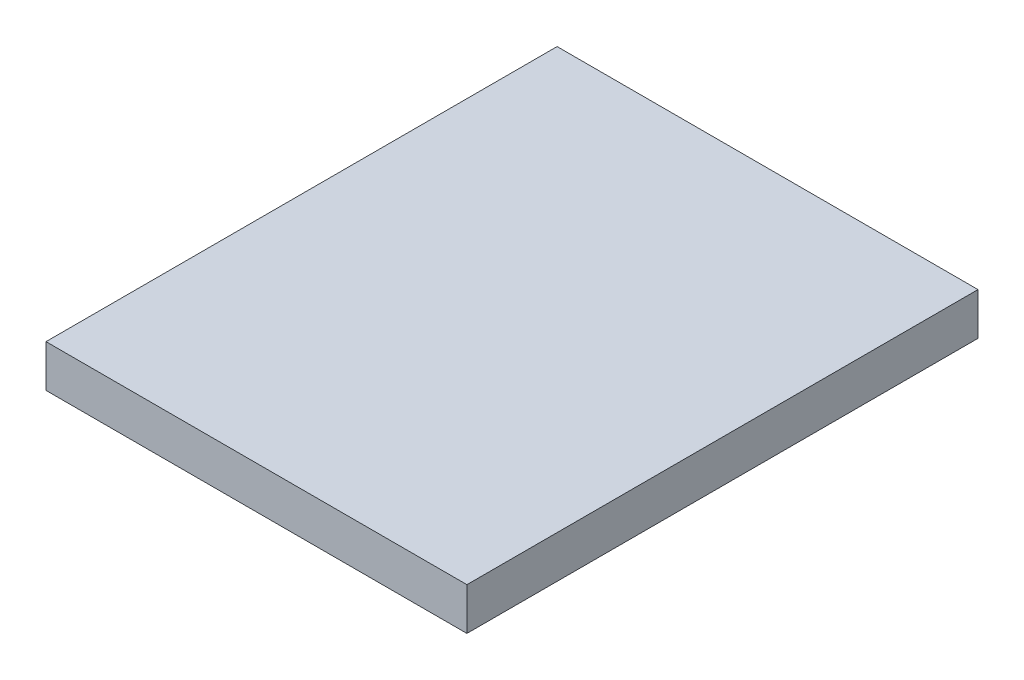
SolidWorks part; units mm, degrees
ref_plane "Front Plane" through (0, 0, 0) normal (0, 0, 1) x (1, 0, 0)
ref_plane "Top Plane" through (0, 0, 0) normal (0, 1, 0) x (1, 0, 0)
ref_plane "Right Plane" through (0, 0, 0) normal (1, 0, 0) x (0, 0, -1)
sketch "Sketch1" plane through (0, 0, 0) normal (0, 1, 0) x (1, 0, 0)
  line L1 (0, 0) -> (127, 0)
  line L2 (0, 0) -> (0, 154.21)
  line L3 (0, 154.21) -> (127, 154.21)
  line L4 (127, 0) -> (127, 154.21)
extrude "Boss-Extrude1" add sketch "Sketch1" along normal blind 12.75
ref_plane "Plane1" through (63.5, 0, 0) normal (-1, 0, 0) x (0, 0, 1)
